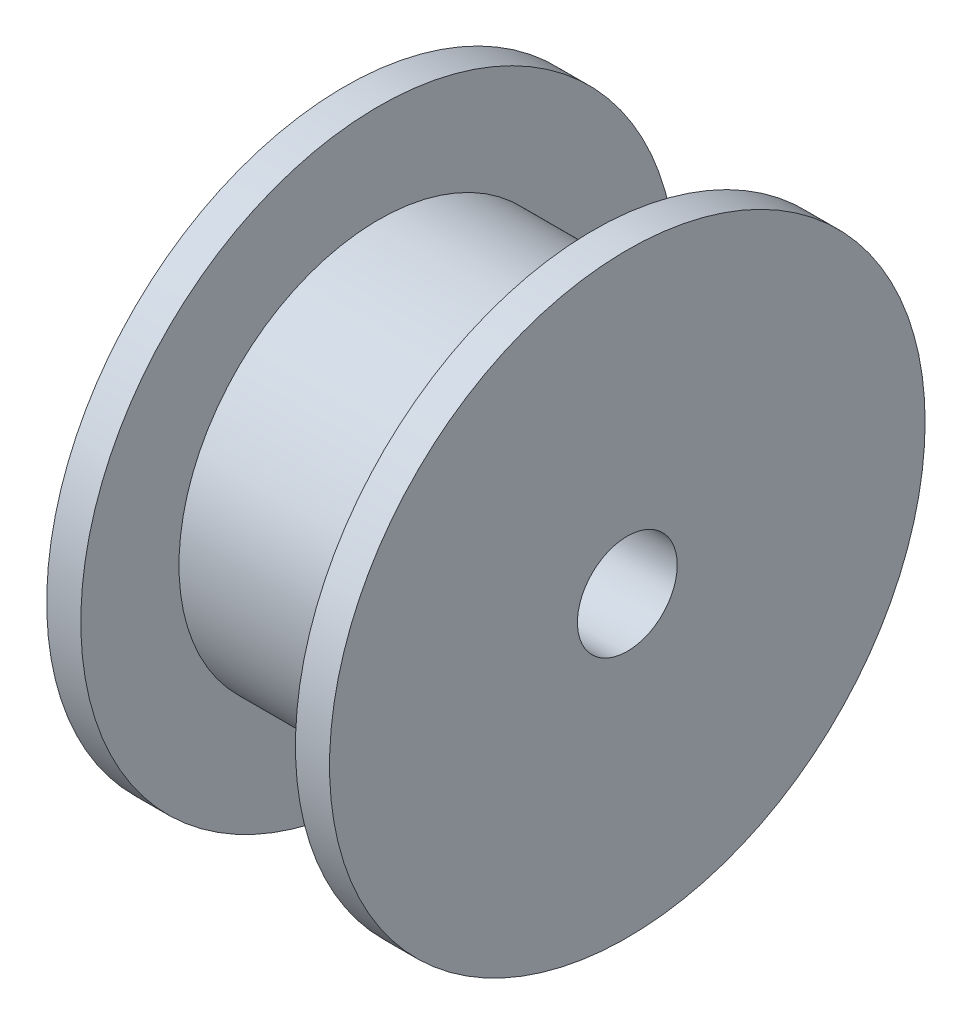
SolidWorks part; units mm, degrees
material "6061-T6 (SS)"
ref_plane "Front Plane" through (0, 0, 0) normal (0, 0, 1) x (1, 0, 0)
ref_plane "Top Plane" through (0, 0, 0) normal (0, 1, 0) x (1, 0, 0)
ref_plane "Right Plane" through (0, 0, 0) normal (1, 0, 0) x (0, 0, -1)
sketch "Sketch1" plane through (0, 0, 0) normal (0, 0, 1) x (1, 0, 0)
  line L0 (8.2688, 8.95) -> (8.2688, 1.5)
  line L1 (8.2688, 8.95) -> (9.2938, 8.95)
  line L2 (9.2938, 8.95) -> (9.2938, 6)
  line L3 (9.2938, 6) -> (15.7438, 6)
  line L4 (15.7438, 6) -> (15.7438, 8.95)
  line L5 (15.7438, 8.95) -> (16.7688, 8.95)
  line L6 (16.7688, 8.95) -> (16.7688, 1.5)
  line L7 (16.7688, 1.5) -> (8.2688, 1.5)
  line L8 (0, 0) -> (-7.6744, 0) construction
  dimension "D1" = 3
  dimension "D2" = 17.9
  dimension "D3" = 12
  dimension "D4" = 6.45
  dimension "D5" = 8.5
  dimension "D6" = 8.2688
revolve "Revolve1" add sketch "Sketch1" angle 360 about L8
ref_plane "Plano1" through (12.5188, 0, 0) normal (1, 0, 0) x (0, 0, -1)
